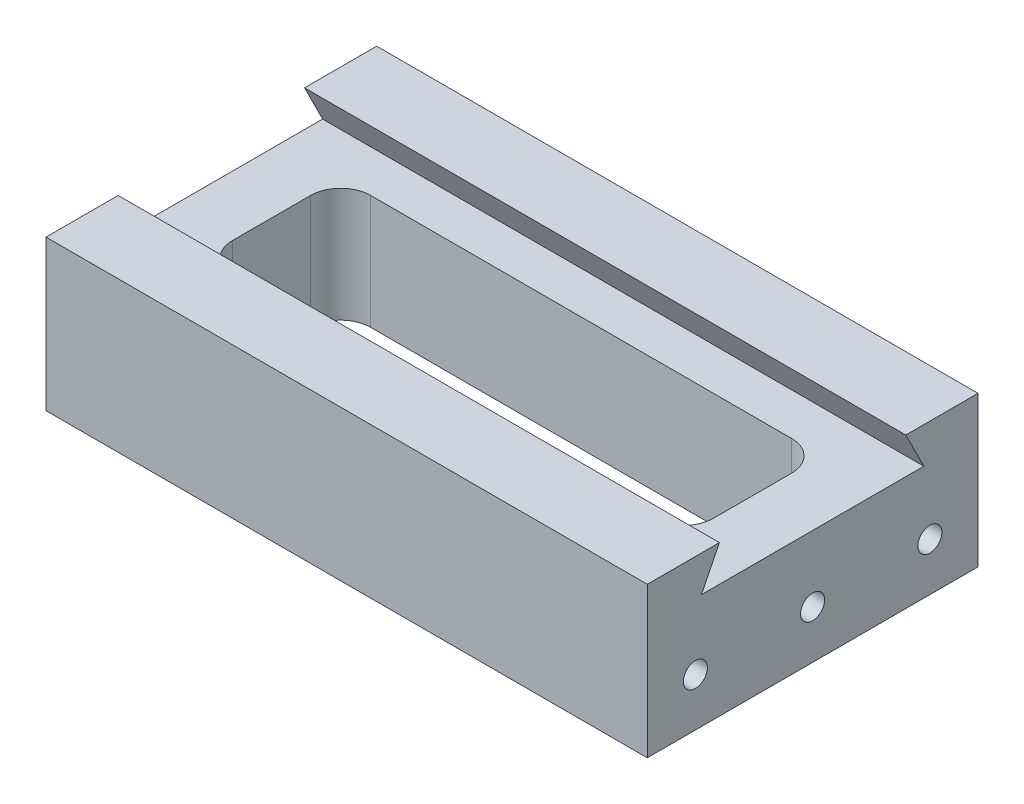
SolidWorks part; units mm, degrees
material "Plain Carbon Steel"
ref_plane "Front Plane" through (0, 0, 0) normal (0, 0, 1) x (1, 0, 0)
ref_plane "Top Plane" through (0, 0, 0) normal (0, 1, 0) x (1, 0, 0)
ref_plane "Right Plane" through (0, 0, 0) normal (1, 0, 0) x (0, 0, -1)
sketch "Sketch1" plane through (0, 0, 0) normal (1, 0, 0) x (0, 0, -1)
  line L0 (9, 19) -> (46, 19)
  line L1 (0, 0) -> (55, 0)
  line L2 (0, 0) -> (0, 25)
  line L3 (0, 25) -> (12, 25)
  line L4 (55, 0) -> (55, 25)
  line L5 (9, 19) -> (12, 25)
  line L6 (46, 19) -> (43, 25)
  line L7 (43, 25) -> (55, 25)
  point P5 (12, 25)
  point P6 (43, 25)
  point P9 (27.5, 19)
  point P10 (27.5, 25)
  dimension "D1" = 55
  dimension "D2" = 25
  dimension "D3" = 12
  dimension "D4" = 12
  dimension "D5" = 37
  dimension "D6" = 6
  dimension "D7" = 9
extrude "Boss-Extrude1" add sketch "Sketch1" along normal mid plane 100
hole_wizard "Tap Drill for M5x0.8 Tap1" positions "3DSketch5" profile "Sketch5" hole size "M5x0.8" standard "ANSI Metric"
sketch3d "3DSketch5"
  line L0 (50, 25, 0) -> (50, 0, 0) construction
  line L1 (50, 0, 0) -> (50, 0, -55) construction
  point P0 (50, 8, -8)
  point P2 (50, 8, -27.5)
  point P4 (50, 8, -47)
  dimension "D1" = 8
  dimension "D2" = 8
  dimension "D3" = 27.5
  dimension "D4" = 8
  dimension "D5" = 47
sketch "Sketch5" plane through (50, 8, -8) normal (0, 1, 0) x (0, 0, -1)
  line L0 (0, 0) -> (0, 8.4017)
  line L1 (0, 8.4017) -> (2, 7.2)
  line L2 (2, 7.2) -> (2, 0)
  line L5 (2, 0) -> (0, 0)
  line L10 (0, 8.4017) -> (-2, 7.2) construction
  line L11 (0, -6.35) -> (0, 107.95) construction
  dimension "Hole Dia." = 4
  dimension "Hole Depth" = 7.2
  dimension "Drill Angle" = 118
ref_plane "Plane1" through (0, 0, 0) normal (1, 0, 0) x (0, 0, -1)
mirror "Mirror2" about plane through (0, 0, 0) normal (1, 0, 0) of "Tap Drill for M5x0.8 Tap1"
ref_plane "Plane2" through (0, 19, 0) normal (0, 1, 0) x (1, 0, 0)
sketch "Sketch6" plane through (0, 19, 0) normal (0, 1, 0) x (1, 0, 0)
  line L0 (-50, 12) -> (-50, 0) construction
  line L1 (-50, 0) -> (50, 0) construction
  line L2 (50, 0) -> (50, 12) construction
  line L3 (50, 12) -> (-50, 12) construction
  line L4 (-50, 46) -> (-50, 9) construction
  line L5 (-50, 9) -> (50, 9) construction
  line L6 (50, 9) -> (50, 46) construction
  line L7 (50, 46) -> (-50, 46) construction
  line L8 (-50, 55) -> (-50, 43) construction
  line L9 (-50, 43) -> (50, 43) construction
  line L10 (50, 43) -> (50, 55) construction
  line L11 (50, 55) -> (-50, 55) construction
  line L12 (-50, 12) -> (-50, 0)
  line L13 (-50, 0) -> (50, 0)
  line L14 (50, 0) -> (50, 12)
  line L15 (50, 12) -> (-50, 12)
  line L16 (-50, 46) -> (-50, 9)
  line L17 (-50, 9) -> (50, 9)
  line L18 (50, 9) -> (50, 46)
  line L19 (50, 46) -> (-50, 46)
  line L20 (-50, 55) -> (-50, 43)
  line L21 (-50, 43) -> (50, 43)
  line L22 (50, 43) -> (50, 55)
  line L23 (50, 55) -> (-50, 55)
  line L25 (-35, 39) -> (35, 39)
  line L26 (-40, 34) -> (-40, 21)
  line L27 (-35, 16) -> (35, 16)
  line L28 (40, 34) -> (40, 21)
  arc A0 (35, 39) -> (40, 34) centre (35, 34) cw
  arc A1 (35, 16) -> (40, 21) centre (35, 21) ccw
  arc A2 (-40, 21) -> (-35, 16) centre (-35, 21) ccw
  arc A3 (-35, 39) -> (-40, 34) centre (-35, 34) ccw
  point P10 (0, 55)
  point P12 (0, 39)
  point P18 (40, 39)
  point P23 (40, 16)
  point P28 (-40, 39)
  point P29 (-40, 27.5)
  point P30 (-50, 27.5)
  dimension "D4" = 5
  dimension "D1" = 80
  dimension "D2" = 23
extrude "Cut-Extrude1" cut sketch "Sketch6" against normal through all contours L25 A3 L26 A2 L27 A1 L28 A0
